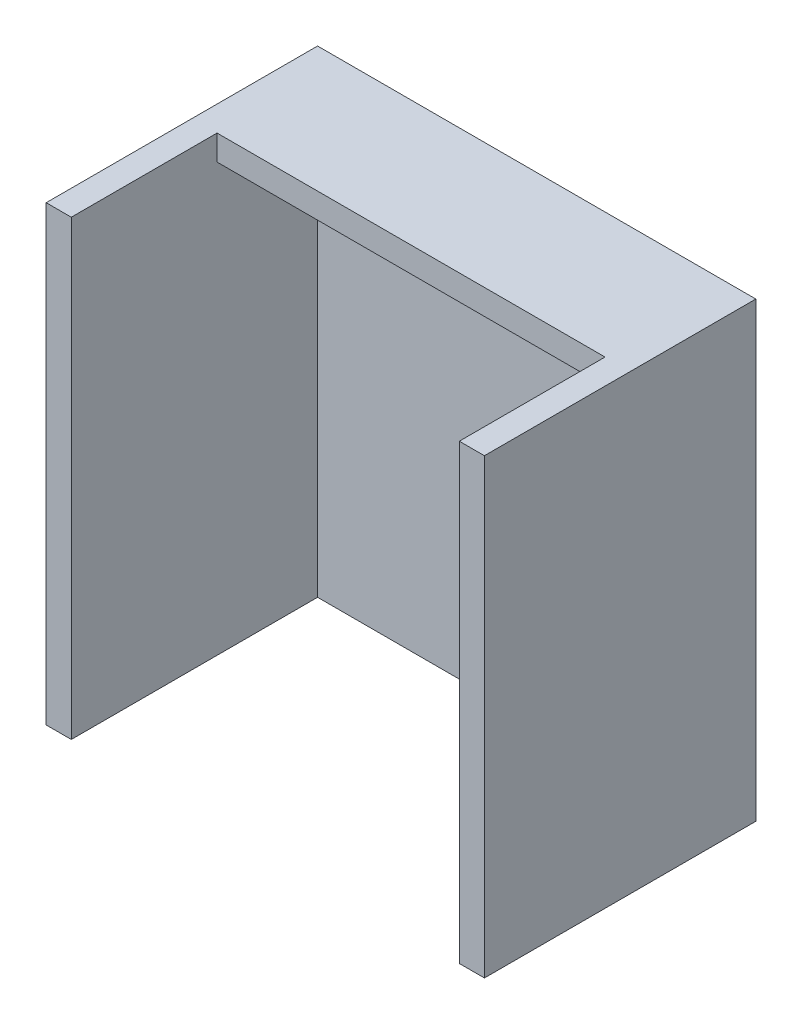
SolidWorks part; units mm, degrees
ref_plane "Front Plane" through (0, 0, 0) normal (0, 0, 1) x (1, 0, 0)
ref_plane "Top Plane" through (0, 0, 0) normal (0, 1, 0) x (1, 0, 0)
ref_plane "Right Plane" through (0, 0, 0) normal (1, 0, 0) x (0, 0, -1)
sketch "Sketch1" plane through (0, 0, 0) normal (0, 0, 1) x (1, 0, 0)
  line L1 (34.036, -23.368) -> (34.036, 33.782)
  line L8 (-21.336, 33.782) -> (34.036, 33.782)
  line L9 (-21.336, -23.368) -> (-21.336, 33.782)
  line L10 (-21.336, -23.368) -> (34.036, -23.368)
  point P2 (0, 0)
  dimension "D1" = 55.372
  dimension "D2" = 57.15
extrude "Boss-Extrude1" add sketch "Sketch1" along normal blind 34.29
shell "Shell1" thickness 3.175
sketch "Sketch2" plane through (0, 30.607, 0) normal (0, -1, 0) x (1, 0, 0)
  line L0 (10.5646, 3.175) -> (10.5646, 15.875)
  line L1 (30.861, 3.175) -> (-18.161, 3.175) construction
  line L2 (10.5646, 15.875) -> (-18.161, 15.875)
  line L3 (-18.161, 34.29) -> (-18.161, 3.175) construction
  line L5 (-18.161, 15.875) -> (30.861, 15.875)
  line L6 (-18.161, 15.875) -> (-18.161, 34.29)
  line L7 (-18.161, 34.29) -> (30.861, 34.29)
  line L8 (30.861, 15.875) -> (30.861, 34.29)
  line M2 (30.861, 3.175) -> (30.861, 34.29)
  line M3 (30.861, 34.29) -> (-18.161, 34.29)
  line M4 (-18.161, 34.29) -> (-18.161, 3.175)
extrude "Cut-Extrude1" cut sketch "Sketch2" against normal blind 39.116 contours L2 L5 M2 M3 M4
ref_plane "Plane1" through (6.35, 0, 0) normal (-1, 0, 0) x (0, 0, 1)
